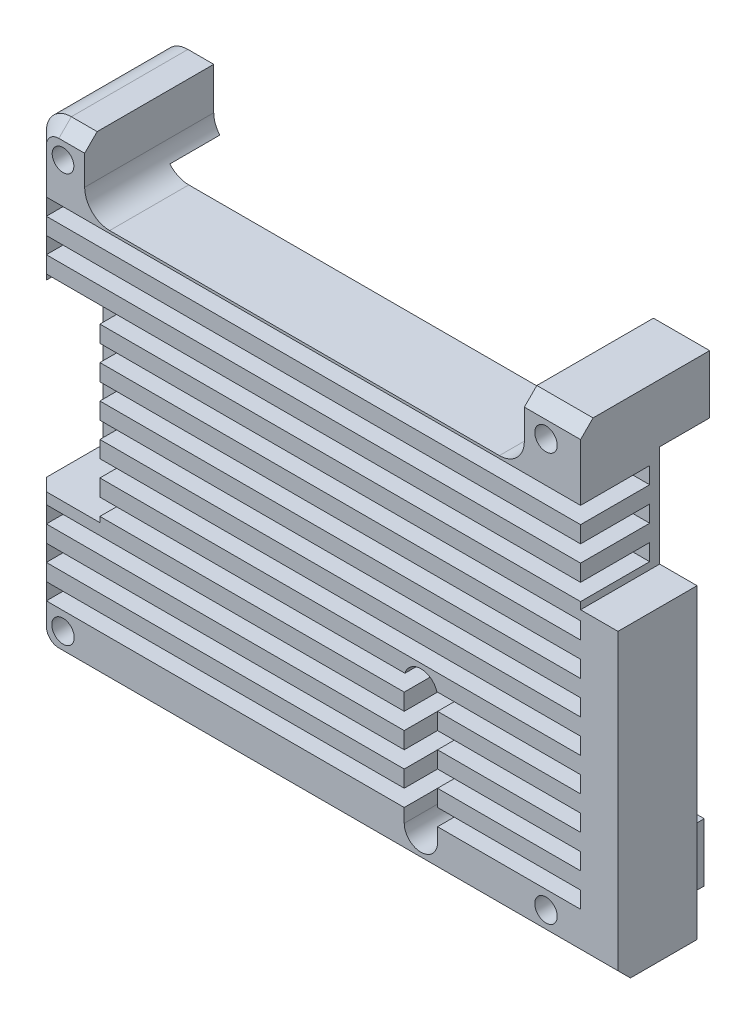
SolidWorks part; units mm, degrees
ref_plane "Front Plane" through (0, 0, 0) normal (0, 0, 1) x (1, 0, 0)
ref_plane "Top Plane" through (0, 0, 0) normal (0, 1, 0) x (1, 0, 0)
ref_plane "Right Plane" through (0, 0, 0) normal (1, 0, 0) x (0, 0, -1)
sketch "Sketch1" plane through (0, 0, 0) normal (0, 0, 1) x (1, 0, 0)
  line L0 (15.4, 22.46) -> (15.4, 26.54) construction
  line L1 (-36.4, 28) -> (16.4, 28)
  line L2 (-36.4, 28) -> (-36.4, 19.96)
  line L3 (-36.4, 19.96) -> (16.4, 19.96)
  line L4 (-39.5, -28) -> (39.5, -28)
  line L5 (42.5, -25) -> (42.5, 25)
  line L6 (39.5, 28) -> (-39.5, 28)
  line L7 (-42.5, 25) -> (-42.5, -25)
  line L8 (-39.5, -28) -> (39.5, -28)
  line L9 (42.5, -25) -> (42.5, 25)
  line L10 (39.5, 28) -> (-39.5, 28)
  line L11 (-42.5, 25) -> (-42.5, -25)
  line L12 (16.4, 28) -> (16.4, 19.96)
  line L13 (13.31, 21.96) -> (14.9, 21.96) construction
  line L14 (-35.4, 26.54) -> (-35.4, 22.46) construction
  line L15 (23.15, 28) -> (23.15, 8.8)
  line L16 (23.15, 8.8) -> (27.64, 8.8)
  line L17 (27.64, 8.8) -> (27.64, -28)
  line L18 (24.15, 10) -> (24.15, 25.5) construction
  line L19 (45.3, 9.8) -> (24.35, 9.8) construction
  line L20 (28.64, -3.8) -> (28.64, 2) construction
  line L21 (3.975, -5.26) -> (3.975, -27.66) construction
  line L22 (2.85, -5.26) -> (5.1, -5.26) construction
  line L23 (5.1, -27.66) -> (2.85, -27.66) construction
  line L24 (3.975, -8.92) -> (3.975, -24) construction
  line L25 (5.975, -8.92) -> (5.975, -24)
  line L26 (1.975, -8.92) -> (1.975, -24)
  line L27 (16.8644, 21.05) -> (21.1444, 15.97) construction
  line L28 (-38.535, 11.2) -> (-38.535, -11.2) construction
  line L29 (22.0044, 21.51) -> (16.0044, 21.51)
  line L30 (22.0044, 21.51) -> (22.0044, 15.51)
  line L31 (22.0044, 15.51) -> (16.0044, 15.51)
  line L32 (16.0044, 21.51) -> (16.0044, 15.51)
  line L33 (22.0044, 21.51) -> (16.0044, 15.51) construction
  line L34 (22.0044, 15.51) -> (16.0044, 21.51) construction
  line L35 (-39.66, 11.2) -> (-37.41, 11.2) construction
  line L36 (-37.41, -11.2) -> (-39.66, -11.2) construction
  line L37 (-38.535, 7.54) -> (-38.535, -7.54) construction
  line L38 (-36.535, 7.54) -> (-36.535, -7.54)
  line L39 (-40.535, 7.54) -> (-40.535, -7.54)
  circle A0 centre (19, 24.5) radius 1.35 construction
  circle A1 centre (-39, 24.5) radius 1.3 construction
  circle A2 centre (-39, -24.5) radius 1.35 construction
  circle A3 centre (19, -24.5) radius 1.35 construction
  arc A4 (-42.5, -25) -> (-39.5, -28) centre (-39.5, -25) ccw
  arc A5 (39.5, -28) -> (42.5, -25) centre (39.5, -25) ccw
  arc A6 (42.5, 25) -> (39.5, 28) centre (39.5, 25) ccw
  arc A7 (-39.5, 28) -> (-42.5, 25) centre (-39.5, 25) ccw
  arc A8 (-42.5, -25) -> (-39.5, -28) centre (-39.5, -25) ccw
  arc A9 (39.5, -28) -> (42.5, -25) centre (39.5, -25) ccw
  arc A10 (42.5, 25) -> (39.5, 28) centre (39.5, 25) ccw
  arc A11 (-39.5, 28) -> (-42.5, 25) centre (-39.5, 25) ccw
  circle A12 centre (19, 24.5) radius 1.35
  circle A13 centre (-39, 24.5) radius 1.3
  circle A14 centre (-39, -24.5) radius 1.35
  circle A15 centre (19, -24.5) radius 1.35
  arc A16 (5.975, -8.92) -> (1.975, -8.92) centre (3.975, -8.92) ccw
  arc A17 (1.975, -24) -> (5.975, -24) centre (3.975, -24) ccw
  arc A18 (-36.535, 7.54) -> (-40.535, 7.54) centre (-38.535, 7.54) ccw
  arc A19 (-40.535, -7.54) -> (-36.535, -7.54) centre (-38.535, -7.54) ccw
  point P52 (3.975, -16.46)
  point P57 (3.975, -22)
  point P61 (3.975, -26)
  point P62 (19.0044, 18.51)
  point P78 (-38.535, 0)
  dimension "D2" = 1
  dimension "D3" = 2
  dimension "D4" = 1
  dimension "D5" = 1
  dimension "D6" = 1
  dimension "D7" = 1
  dimension "D8" = 2
  dimension "D9" = 4
  dimension "D10" = 6
  dimension "D1" = 0
extrude "Boss-Extrude1" add sketch "Sketch1" along normal blind 15.5 contours L10 A11 L11 A8 L8 L17 L16 L15 L12 L29 L30 L31 L32 L3 L2 A19 L39 A18 L38 A17 L26 A16 L25 A15 A14 A13 A12 | L3 L32 L31 L30 L29 L12
sketch "Sketch2" plane through (0, 0, 0) normal (0, 0, -1) x (-1, 0, 0)
  line L0 (-16.4, 21) -> (-23.15, 21)
  line L1 (36.4, 21) -> (42.5, 21)
  line L3 (-22.5, -21) -> (-15.5, -21)
  line L4 (-22.5, -21) -> (-22.5, -28)
  line L5 (-22.5, -28) -> (-15.5, -28)
  line L6 (-15.5, -21) -> (-15.5, -28)
  line L7 (-22.5, -21) -> (-15.5, -28) construction
  line L8 (-22.5, -28) -> (-15.5, -21) construction
  line L9 (42.5, -21) -> (35.5, -21)
  line L10 (-16.4, 19.96) -> (-16.4, 28)
  line L11 (-16.4, 28) -> (-23.15, 28)
  line L12 (-23.15, 28) -> (-23.15, 8.8)
  line L13 (-23.15, 8.8) -> (-27.64, 8.8)
  line L14 (-27.64, 8.8) -> (-27.64, -28)
  line L15 (-27.64, -28) -> (39.5, -28)
  line L16 (42.5, -25) -> (42.5, 25)
  line L17 (39.5, 28) -> (36.4, 28)
  line L18 (36.4, 28) -> (36.4, 19.96)
  line L19 (36.4, 19.96) -> (-16.4, 19.96)
  line L20 (-16.4, 19.96) -> (-16.4, 28)
  line L21 (-16.4, 28) -> (-23.15, 28)
  line L22 (-23.15, 28) -> (-23.15, 8.8)
  line L23 (-23.15, 8.8) -> (-27.64, 8.8)
  line L24 (-27.64, 8.8) -> (-27.64, -28)
  line L25 (-27.64, -28) -> (39.5, -28)
  line L26 (42.5, -25) -> (42.5, 25)
  line L27 (39.5, 28) -> (36.4, 28)
  line L28 (36.4, 28) -> (36.4, 19.96)
  line L29 (36.4, 19.96) -> (-16.4, 19.96)
  line L30 (42.5, -21) -> (42.5, -28)
  line L31 (42.5, -28) -> (35.5, -28)
  line L32 (35.5, -21) -> (35.5, -28)
  line L33 (42.5, -21) -> (35.5, -28) construction
  line L34 (42.5, -28) -> (35.5, -21) construction
  arc A2 (39.5, -28) -> (42.5, -25) centre (39.5, -25) ccw
  arc A3 (42.5, 25) -> (39.5, 28) centre (39.5, 25) ccw
  arc A4 (39.5, -28) -> (42.5, -25) centre (39.5, -25) ccw
  arc A5 (42.5, 25) -> (39.5, 28) centre (39.5, 25) ccw
  point P13 (-19, -24.5)
  point P22 (39, -24.5)
  line M23 (-16.4, 19.96) -> (-16.4, 28)
  line M25 (-23.15, 28) -> (-23.15, 8.8)
  line M26 (-23.15, 8.8) -> (-27.64, 8.8)
  line M27 (-27.64, 8.8) -> (-27.64, -28)
  line M28 (-27.64, -28) -> (39.5, -28)
  line M30 (42.5, -25) -> (42.5, 25)
  line M33 (36.4, 28) -> (36.4, 19.96)
  line M34 (36.4, 19.96) -> (-16.4, 19.96)
  arc M35 (40.535, -7.54) -> (36.535, -7.54) centre (38.535, -7.54) cw
  line M36 (36.535, -7.54) -> (36.535, 7.54)
  arc M37 (36.535, 7.54) -> (40.535, 7.54) centre (38.535, 7.54) cw
  line M38 (40.535, 7.54) -> (40.535, -7.54)
  arc M39 (-1.975, -24) -> (-5.975, -24) centre (-3.975, -24) cw
  line M40 (-5.975, -24) -> (-5.975, -8.92)
  arc M41 (-5.975, -8.92) -> (-1.975, -8.92) centre (-3.975, -8.92) cw
  line M42 (-1.975, -8.92) -> (-1.975, -24)
  dimension "D2" = 7
  dimension "D1" = 0
extrude "Cut-Extrude1" cut sketch "Sketch2" against normal blind 6 contours L32 L9 L1 L0 L4 L3 L6 M30 M33 M34 M23 M25 M26 M27 M28 M38 M35 M36 M37 M42 M39 M40 M41
fillet "Fillet1" radius 3 2 edges at (-36.4, 19.96, 10.75) (16.4, 19.96, 10.75)
chamfer "Chamfer1" distance 1.5 angle 45 6 edges at (-5.93, -28, 15.5) (-41.6213, -27.1213, 15.5) (-42.5, 0, 15.5) (-41.6213, 27.1213, 15.5) (-37.95, 28, 15.5) (19.775, 28, 15.5)
sketch "Sketch3" plane through (0, 0, 15.5) normal (0, 0, 1) x (1, 0, 0)
  line L0 (-38.535, 9.54) -> (-38.535, -9.54) construction
  line L1 (-42.5, -25) -> (-42.5, 25) construction
  line L2 (-34.57, -11) -> (-42.5, -11)
  line L3 (-34.57, -11) -> (-34.57, 11)
  line L4 (-34.57, 11) -> (-42.5, 11)
  line L5 (-42.5, -11) -> (-42.5, 11)
  line L6 (-34.57, -11) -> (-42.5, 11) construction
  line L7 (-34.57, 11) -> (-42.5, -11) construction
  arc A0 (-36.535, 7.54) -> (-40.535, 7.54) centre (-38.535, 7.54) ccw construction
  arc A1 (-40.535, -7.54) -> (-36.535, -7.54) centre (-38.535, -7.54) ccw construction
  point P8 (-38.535, 0)
  dimension "D1" = 22
extrude "Cut-Extrude2" cut sketch "Sketch3" against normal blind 8.3
sketch "Sketch4" plane through (0, 0, 15.5) normal (0, 0, 1) x (1, 0, 0)
  line L0 (-41, 25) -> (-41, 11) construction
  line L1 (-41, 19.65) -> (23.15, 19.65)
  line L2 (-41, 19.65) -> (-41, 17.65)
  line L3 (-41, 17.65) -> (23.15, 17.65)
  line L4 (23.15, 19.65) -> (23.15, 17.65)
  line L5 (23.15, 26.5) -> (23.15, 8.8) construction
  line L6 (-41, 13.65) -> (23.15, 13.65)
  line L7 (23.15, 15.65) -> (23.15, 13.65)
  line L8 (-41, 15.65) -> (23.15, 15.65)
  line L9 (-41, 15.65) -> (-41, 13.65)
  line L10 (-41, 9.65) -> (23.15, 9.65)
  line L11 (23.15, 11.65) -> (23.15, 9.65)
  line L12 (-41, 11.65) -> (23.15, 11.65)
  line L13 (-41, 11.65) -> (-41, 9.65)
  line L14 (-41, 5.65) -> (23.15, 5.65)
  line L15 (23.15, 7.65) -> (23.15, 5.65)
  line L16 (-41, 7.65) -> (23.15, 7.65)
  line L17 (-41, 7.65) -> (-41, 5.65)
  line L18 (-41, 1.65) -> (23.15, 1.65)
  line L19 (23.15, 3.65) -> (23.15, 1.65)
  line L20 (-41, 3.65) -> (23.15, 3.65)
  line L21 (-41, 3.65) -> (-41, 1.65)
  line L22 (-41, -2.35) -> (23.15, -2.35)
  line L23 (23.15, -0.35) -> (23.15, -2.35)
  line L24 (-41, -0.35) -> (23.15, -0.35)
  line L25 (-41, -0.35) -> (-41, -2.35)
  line L26 (-41, -6.35) -> (23.15, -6.35)
  line L27 (23.15, -4.35) -> (23.15, -6.35)
  line L28 (-41, -4.35) -> (23.15, -4.35)
  line L29 (-41, -4.35) -> (-41, -6.35)
  line L30 (-41, -10.35) -> (23.15, -10.35)
  line L31 (23.15, -8.35) -> (23.15, -10.35)
  line L32 (-41, -8.35) -> (23.15, -8.35)
  line L33 (-41, -8.35) -> (-41, -10.35)
  line L34 (-41, -14.35) -> (23.15, -14.35)
  line L35 (23.15, -12.35) -> (23.15, -14.35)
  line L36 (-41, -12.35) -> (23.15, -12.35)
  line L37 (-41, -12.35) -> (-41, -14.35)
  line L38 (-41, -18.35) -> (23.15, -18.35)
  line L39 (23.15, -16.35) -> (23.15, -18.35)
  line L40 (-41, -16.35) -> (23.15, -16.35)
  line L41 (-41, -16.35) -> (-41, -18.35)
  line L42 (-41, -22.35) -> (23.15, -22.35)
  line L43 (23.15, -20.35) -> (23.15, -22.35)
  line L44 (-41, -20.35) -> (23.15, -20.35)
  line L45 (-41, -20.35) -> (-41, -22.35)
  dimension "D1" = 2
  dimension "D3" = 4
  dimension "D2" = 11
extrude "Cut-Extrude3" cut sketch "Sketch4" against normal up to surface (8.3 mm away) up to face at (-38.535, 0, 7.2)
